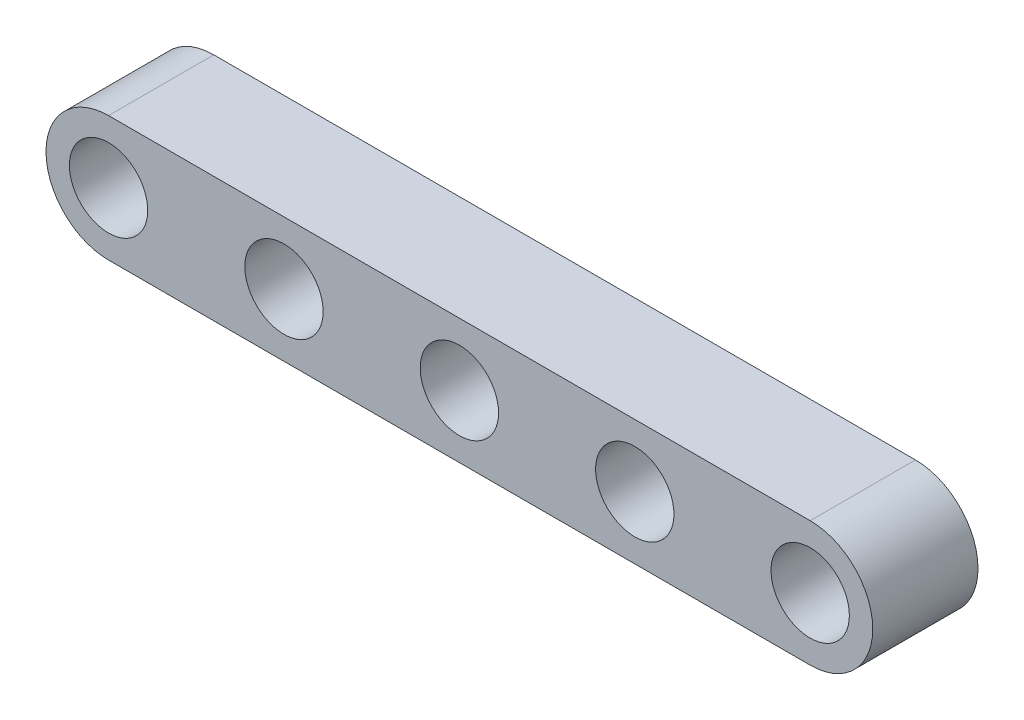
SolidWorks part; units mm, degrees
ref_plane "Front" through (0, 0, 0) normal (0, 0, 1) x (1, 0, 0)
ref_plane "Top" through (0, 0, 0) normal (0, 1, 0) x (1, 0, 0)
ref_plane "Right" through (0, 0, 0) normal (1, 0, 0) x (0, 0, -1)
sketch "Sketch1" plane through (0, 0, 0) normal (0, 0, 1) x (1, 0, 0)
  line L0 (-15, 0) -> (15, 0) construction
  line L1 (-15, 2.675) -> (15, 2.675)
  line L2 (-15, -2.675) -> (15, -2.675)
  arc A0 (-15, 2.675) -> (-15, -2.675) centre (-15, 0) ccw
  arc A1 (15, -2.675) -> (15, 2.675) centre (15, 0) ccw
  circle A2 centre (-15, 0) radius 1.675
  circle A3 centre (-7.5, 0) radius 1.675
  circle A4 centre (0, 0) radius 1.675
  circle A5 centre (7.5, 0) radius 1.675
  circle A6 centre (15, 0) radius 1.675
  point P3 (0, 0)
  dimension "D1" = 3.35
  dimension "D3" = 1
  dimension "D2" = 30
  dimension "D4" = 5
extrude "Boss-Extrude1" add sketch "Sketch1" along normal mid plane 4.5
